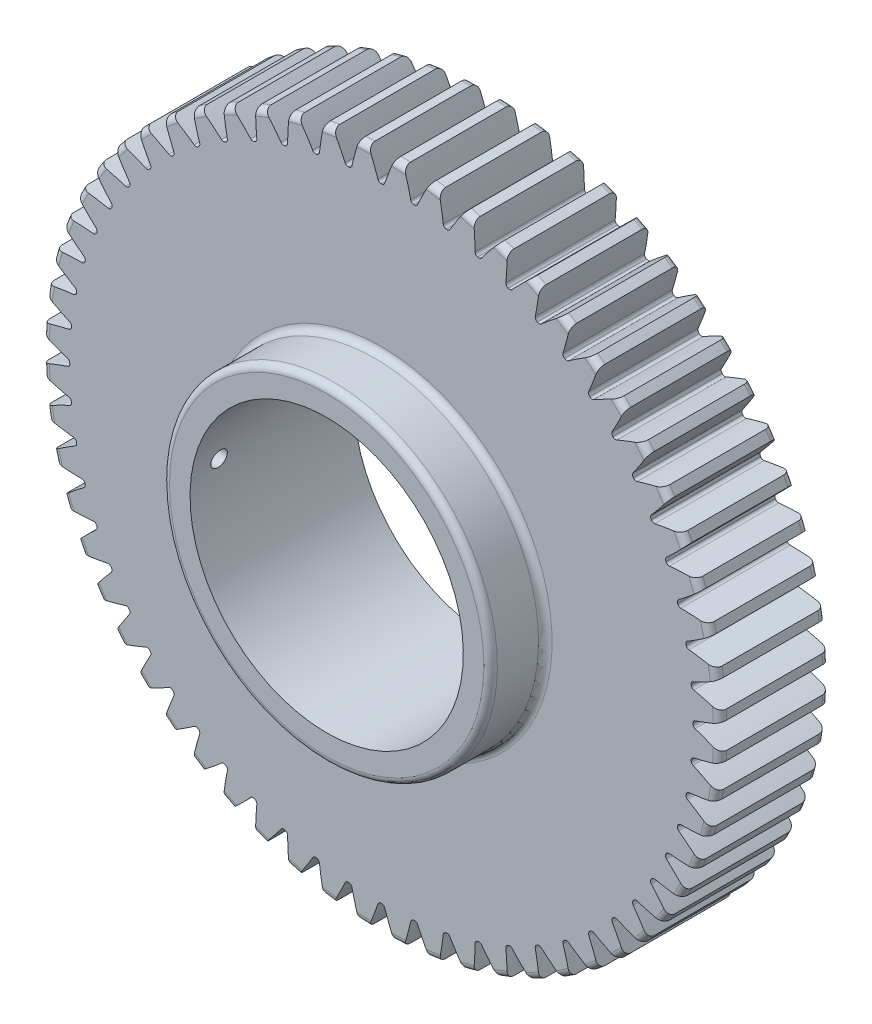
SolidWorks part; units mm, degrees
ref_plane "Front Plane" through (0, 0, 0) normal (0, 0, 1) x (1, 0, 0)
ref_plane "Top Plane" through (0, 0, 0) normal (0, 1, 0) x (1, 0, 0)
ref_plane "Right Plane" through (0, 0, 0) normal (1, 0, 0) x (0, 0, -1)
sketch "Sketch1" plane through (0, 0, 0) normal (0, 0, 1) x (1, 0, 0)
  line L0 (-762, 0) -> (762, 0) construction
  line L1 (0, 0) -> (0, 7.5) construction
  line L2 (-2, 7.2284) -> (-2, 9.3) construction
  line L3 (-2, 9.3) -> (2, 9.3) construction
  line L4 (2, 9.3) -> (2, 7.2284) construction
  line L5 (0, 7.5) -> (0, 9.3) construction
  circle A0 centre (0, 0) radius 62 construction
  circle A1 centre (0, 0) radius 60 construction
  circle A2 centre (0, 0) radius 57 construction
  circle A3 centre (0, 0) radius 30 construction
  circle A4 centre (0, 0) radius 7.5 construction
  dimension "D2" = 2
  dimension "D3" = 5
sketch "Sketch2" plane through (0, 0, 0) normal (1, 0, 0) x (0, 0, -1)
  line L0 (0, 0) -> (-20, 0) construction
  line L1 (-20, 0) -> (-30, 0) construction
  circle A0 centre (-25, 0) radius 2.5
  circle A1 centre (-25, 0) radius 0.4
  dimension "Set Screw Dia" = 5
  dimension "Set Screw Pitch" = 0.8
  dimension "Overall Width" = 30
  dimension "Face Width" = 20
sketch "Sketch4" plane through (0, 0, 0) normal (1, 0, 0) x (0, 0, -1)
  line L0 (-30, 7.5) -> (-30, 30)
  line L1 (-30, 30) -> (-20, 30)
  line L2 (-20, 30) -> (-20, 62)
  line L3 (-20, 62) -> (0, 62)
  line L4 (0, 62) -> (0, 7.5)
  line L5 (-20, 30) -> (-20, 0) construction
  line L6 (0, 62) -> (0, -62) construction
  line L7 (-20, 30) -> (0, 30) construction
  line L12 (-30, 7.5) -> (0, 7.5)
revolve "Revolve1" add sketch "Sketch4" angle 360 about L1
fillet "Fillet2" radius 1.24 4 edges at (0, 30, 30) (0, 30, 20) (0, 62, 20) (0, 62, 0)
sketch "Sketch7" plane through (0, 0, 20) normal (0, 0, 1) x (1, 0, 0)
  line L0 (0, 0) -> (0, 62) construction
  line L1 (1.5706, 59.9794) -> (2.349, 61.9555) construction
  line L3 (3.2448, 61.915) -> (3.1402, 59.9178) construction
  line L4 (3.1402, 59.9178) -> (2.9831, 56.9219) construction
  line L5 (0, 0) -> (2.9831, 56.9219) construction
  line L6 (1.5706, 59.9794) -> (0, 0) construction
  line L7 (1.5706, 59.9794) -> (1.623, 61.9788) construction
  line L8 (1.5706, 59.9794) -> (0, 0) construction
  circle A0 centre (0, 0) radius 62 construction
  arc A1 (-0.0558, 57) -> (0.0558, 57) centre (0, 0) cw
  circle A2 centre (0, 0) radius 57 construction
  arc A3 (-1.5706, 59.9794) -> (1.5706, 59.9794) centre (0, 0) cw construction
  circle A4 centre (0, 0) radius 60 construction
  arc A5 (4.0997, 61.8643) -> (2.3893, 61.9539) centre (0, 0) ccw construction
  arc A6 (1.5706, 59.9794) -> (4.7075, 59.815) centre (0, 0) cw construction
  arc A7 (-2.3893, 61.9539) -> (2.3893, 61.9539) centre (0, 0) cw
  arc A8 (0.6242, 57.4058) -> (2.3893, 61.9539) centre (57.3957, 37.9894) cw
  arc A9 (-0.6242, 57.4058) -> (-2.3893, 61.9539) centre (-57.3957, 37.9894) ccw
  arc A10 (-0.0558, 57) -> (-0.6242, 57.4058) centre (-0.0564, 57.6) cw
  arc A11 (0.0558, 57) -> (0.6242, 57.4058) centre (0.0564, 57.6) ccw
  point P26 (-0.4863, 56.9979)
  point P29 (0.4863, 56.9979)
  dimension "D4" = 0.6
  dimension "D5" = 60
  dimension "D3" = 20
  dimension "D1" = 6.2832
  dimension "D2" = 3.1416
extrude "Cut-Extrude2" cut sketch "Sketch7" against normal through all
pattern_circular "CirPattern1" count 60 over 360 about axis through (0, 0, 0) along (0, 0, 1) of "Cut-Extrude2"
sketch "Sketch8" plane through (0, 0, 30) normal (0, 0, 1) x (1, 0, 0)
  circle A0 centre (0, 0) radius 25
  dimension "D1" = 50
extrude "Cut-Extrude3" cut sketch "Sketch8" against normal through all both and the other way through all
ref_plane "Plane1" through (-25, 0, 0) normal (1, 0, 0) x (0, 0, -1)
sketch "Sketch9" plane through (-25, 0, 0) normal (1, 0, 0) x (0, 0, -1)
  line L0 (-28.76, -30) -> (-28.76, 30) construction
  circle A0 centre (-24.95, 3.5707) radius 1.5
  dimension "D1" = 3
  dimension "D2" = 3.81
extrude "Cut-Extrude4" cut sketch "Sketch9" along normal blind 2.54 and the other way through all
equation "\"D1@Sketch1\"=2.5*(\"Pitch Dia.@Sketch1\"/\"Number of Teeth@Sketch1\")"
equation "\"D1@CirPattern1\"=\"Number of Teeth@Sketch1\""
equation "\"D1@Fillet2\"=\"OD@Sketch1\"*.01"
equation "\"D1@Sketch7\"=3.14159*(\"Pitch Dia.@Sketch1\"/\"Number of Teeth@Sketch1\")"
equation "\"D2@Sketch7\"=\"D1@Sketch7\"/2"
equation "\"D4@Sketch7\"=\"D1@Sketch7\"*.0955"
equation "\"D5@Sketch7\"=\"Pitch Dia.@Sketch1\"/2"
